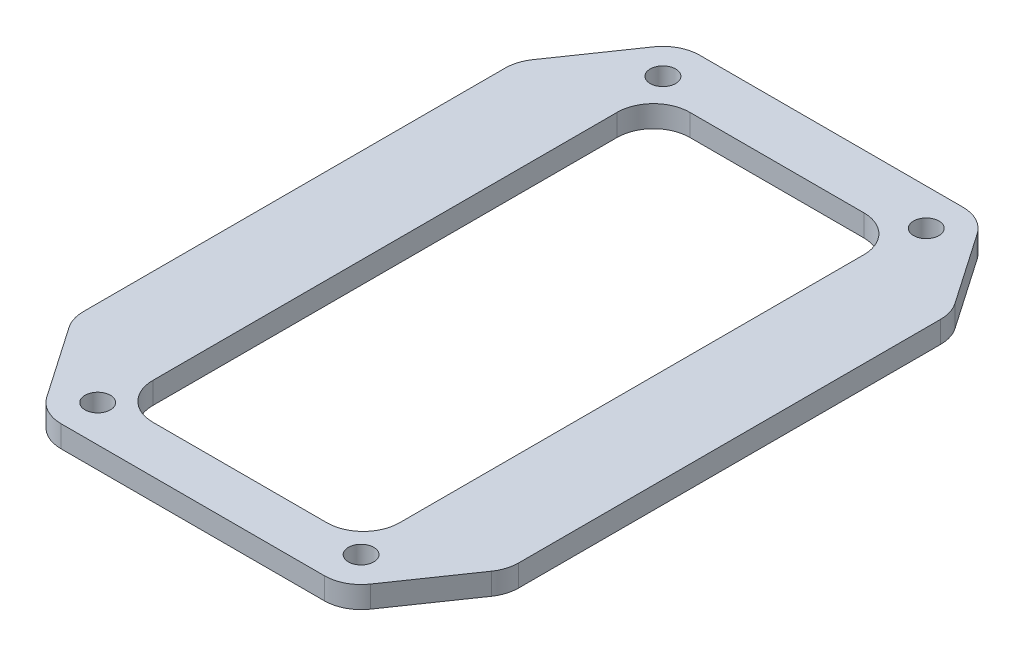
SolidWorks part; units mm, degrees
ref_plane "Front Plane" through (0, 0, 0) normal (0, 0, 1) x (1, 0, 0)
ref_plane "Top Plane" through (0, 0, 0) normal (0, 1, 0) x (1, 0, 0)
ref_plane "Right Plane" through (0, 0, 0) normal (1, 0, 0) x (0, 0, -1)
sketch "Sketch1" plane through (0, 0, 0) normal (0, 1, 0) x (1, 0, 0)
  line L0 (11.85, 82.95) -> (0, 88) construction
  line L1 (0, 0) -> (60, 0)
  line L2 (0, 0) -> (0, 88)
  line L3 (0, 88) -> (60, 88)
  line L4 (60, 0) -> (60, 88)
  line L5 (11.85, 82.95) -> (48.15, 82.95) construction
  line L6 (11.85, 82.95) -> (11.85, 5.05) construction
  line L7 (11.85, 5.05) -> (48.15, 5.05) construction
  line L8 (48.15, 82.95) -> (48.15, 5.05) construction
  line L9 (48.15, 82.95) -> (60, 88) construction
  line L10 (0, 0) -> (11.85, 5.05) construction
  line L11 (48.15, 5.05) -> (60, 0) construction
  line L13 (13, 80.5) -> (47, 80.5)
  line L14 (13, 80.5) -> (13, 6.5)
  line L15 (13, 6.5) -> (47, 6.5)
  line L16 (47, 80.5) -> (47, 6.5)
  circle A0 centre (11.85, 82.95) radius 1.75
  circle A1 centre (48.15, 82.95) radius 1.75
  circle A2 centre (48.15, 5.05) radius 1.75
  circle A3 centre (11.85, 5.05) radius 1.75
  dimension "D5" = 3.5
  dimension "D1" = 60
  dimension "D2" = 88
  dimension "D3" = 77.9
  dimension "D4" = 36.3
  dimension "D6" = 34
  dimension "D7" = 74
  dimension "D8" = 7.5
  dimension "D9" = 13
extrude "Boss-Extrude1" add sketch "Sketch1" along normal blind 3
fillet "Fillet1" radius 5 4 edges at (47, 1.5, -80.5) (47, 1.5, -6.5) (13, 1.5, -6.5) (13, 1.5, -80.5)
sketch "Sketch6" plane through (0, 3, 0) normal (0, 1, 0) x (1, 0, 0)
  line L0 (9.1966, 88) -> (0, 74.65)
  line L5 (60, 88) -> (0, 88) construction
  line L6 (0, 88) -> (0, 0) construction
  line L7 (0, 74.65) -> (0, 13.35)
  line L8 (0, 13.35) -> (9.1966, 0)
  line L9 (0, 0) -> (60, 0) construction
  line L10 (9.1966, 0) -> (50.8034, 0)
  line L11 (50.8034, 0) -> (60, 13.35)
  line L12 (60, 0) -> (60, 88) construction
  line L13 (60, 13.35) -> (60, 74.65)
  line L14 (60, 74.65) -> (50.8034, 88)
  line L15 (50.8034, 88) -> (9.1966, 88)
  line L16 (7.6913, 85.8149) -> (11.85, 82.95) construction
  line L21 (11.85, 82.95) -> (11.85, 88) construction
  line L23 (0, 74.65) -> (60, 74.65) construction
  line L31 (-1, 89) -> (-1, -1)
  line L32 (-1, -1) -> (61, -1)
  line L33 (61, -1) -> (61, 89)
  line L34 (61, 89) -> (-1, 89)
  line L35 (-1, 89) -> (-1, -1)
  line L36 (-1, -1) -> (61, -1)
  line L37 (61, -1) -> (61, 89)
  line L38 (61, 89) -> (-1, 89)
  point P24 (-3.8499, 90.4649)
  dimension "D1" = 61.3
  dimension "D2" = 1
  dimension "D3" = 5.05
extrude "Cut-Extrude3" cut sketch "Sketch6" against normal through all
fillet "Fillet3" radius 5.05 8 edges at (0, 1.5, -74.65) (9.1966, 1.5, -88) (50.8034, 1.5, -88) (60, 1.5, -74.65) (60, 1.5, -13.35) (50.8034, 1.5, 0) (9.1966, 1.5, 0) (0, 1.5, -13.35)
